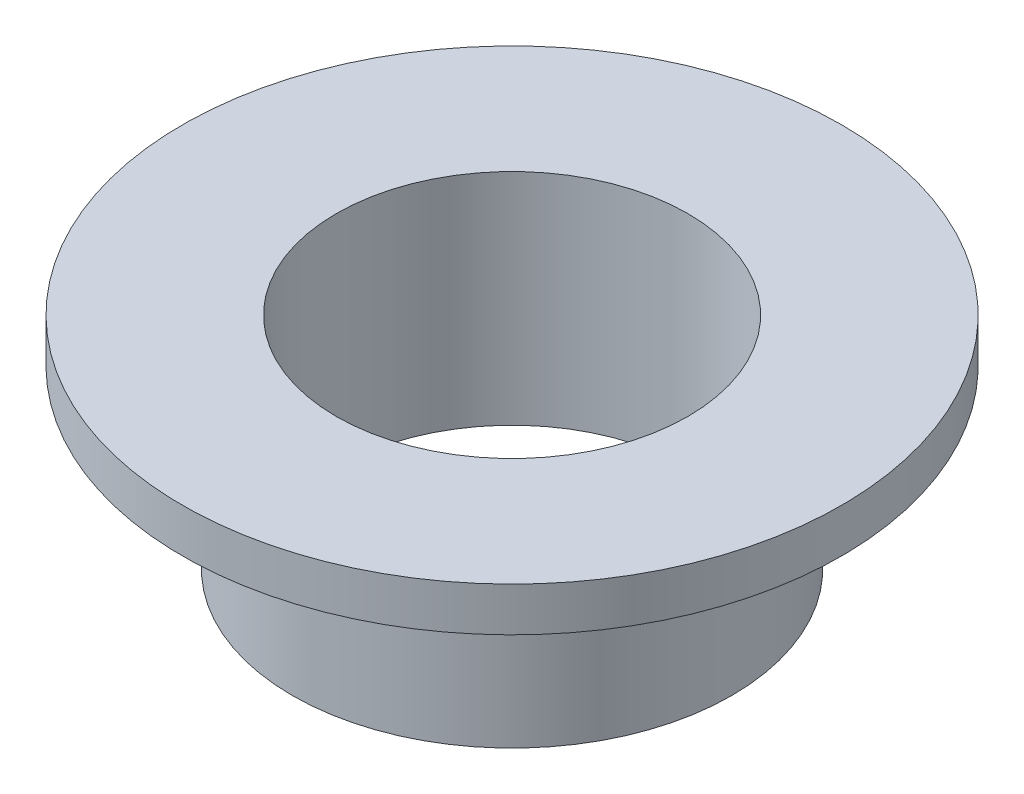
SolidWorks part; units mm, degrees
ref_plane "Plan de face" through (0, 0, 0) normal (0, 0, 1) x (1, 0, 0)
ref_plane "Plan de dessus" through (0, 0, 0) normal (0, 1, 0) x (1, 0, 0)
ref_plane "Plan de droite" through (0, 0, 0) normal (1, 0, 0) x (0, 0, -1)
sketch "Esquisse1" plane through (0, 0, 0) normal (0, 0, 1) x (1, 0, 0)
  line L0 (0, 0) -> (0, 5) construction
  line L1 (-4, 5) -> (-7.5, 5)
  line L2 (-7.5, 5) -> (-7.5, 4)
  line L3 (-7.5, 4) -> (-5, 4)
  line L4 (-5, 4) -> (-5, 0)
  line L5 (-5, 0) -> (-4, 0)
  line L6 (-4, 0) -> (-4, 5)
  dimension "D1" = 5
  dimension "D2" = 4
  dimension "D3" = 5
  dimension "D4" = 1
  dimension "D5" = 7.5
revolve "Révolution1" add sketch "Esquisse1" angle 360 about L0
